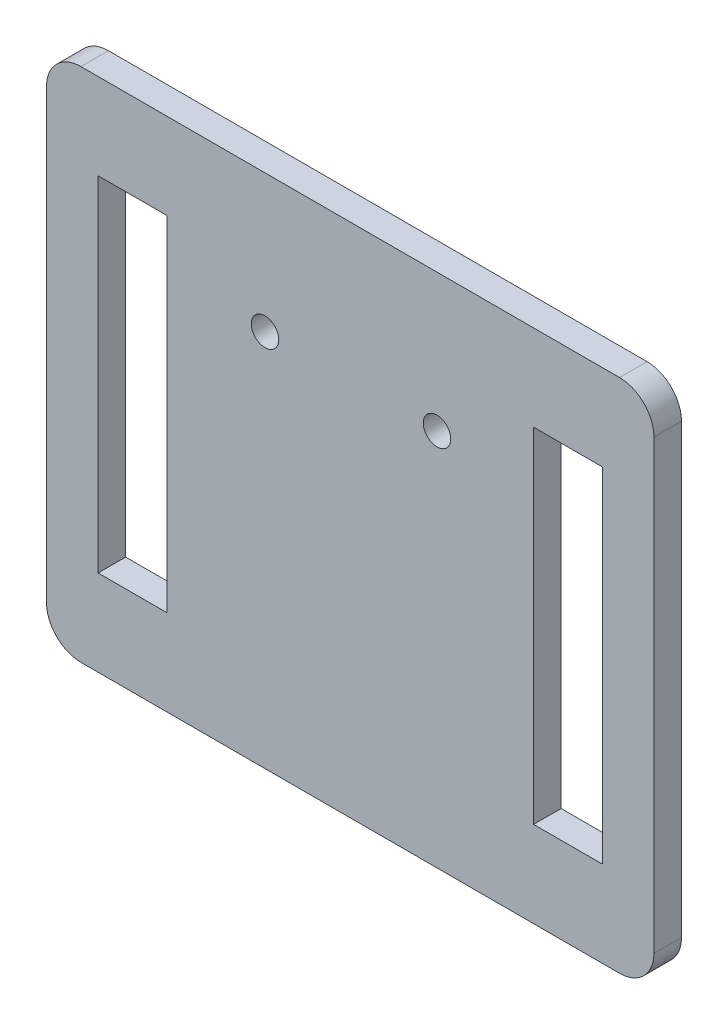
SolidWorks part; units mm, degrees
ref_plane "前视基准面" through (0, 0, 0) normal (0, 0, 1) x (1, 0, 0)
ref_plane "上视基准面" through (0, 0, 0) normal (0, 1, 0) x (1, 0, 0)
ref_plane "右视基准面" through (0, 0, 0) normal (1, 0, 0) x (0, 0, -1)
sketch "草图1" plane through (0, 0, 0) normal (0, 0, 1) x (1, 0, 0)
  line L0 (-985.6155, 3.5) -> (49014.3845, 3.5) construction
  line L1 (1.6819, 11.5) -> (37, 11.5)
  line L2 (1.6819, 11.5) -> (1.6819, -18.5)
  line L3 (37, 11.5) -> (37, -18.5)
  line L4 (1.6819, -18.5) -> (37, -18.5)
  line L15 (-998.3181, -3.5) -> (49001.6819, -3.5) construction
  line L17 (4.6819, 6.5) -> (8.6819, 6.5)
  line L18 (4.6819, 6.5) -> (4.6819, -13.5)
  line L19 (4.6819, -13.5) -> (8.6819, -13.5)
  line L20 (8.6819, 6.5) -> (8.6819, -13.5)
  line L21 (4.6819, 6.5) -> (8.6819, -13.5) construction
  line L22 (4.6819, -13.5) -> (8.6819, 6.5) construction
  line L23 (30, 6.5) -> (34, 6.5)
  line L24 (30, 6.5) -> (30, -13.5)
  line L25 (30, -13.5) -> (34, -13.5)
  line L26 (34, 6.5) -> (34, -13.5)
  line L27 (30, 6.5) -> (34, -13.5) construction
  line L28 (30, -13.5) -> (34, 6.5) construction
  circle A0 centre (14.3845, 3.5) radius 0.8
  circle A1 centre (24.3845, 3.5) radius 0.8
  arc A27 (14.3845, 4.75) -> (14.3845, 2.25) centre (14.3845, 3.5) ccw
  arc A30 (24.3845, 2.25) -> (24.3845, 4.75) centre (24.3845, 3.5) ccw
  point P7 (6.6819, -3.5)
  point P11 (1.6819, -3.5)
  point P17 (32, -3.5)
  dimension "D1" = 1.6
  dimension "D2" = 1.6
  dimension "D3" = 30
  dimension "D4" = 20
  dimension "D7" = 20
  dimension "D8" = 3
  dimension "D9" = 3
  dimension "D10" = 4
  dimension "D11" = 4
extrude "凸台-拉伸1" add sketch "草图1" along normal blind 1.6
fillet "圆角1" radius 2 4 edges at (37, -18.5, 0.8) (1.6819, -18.5, 0.8) (1.6819, 11.5, 0.8) (37, 11.5, 0.8)
